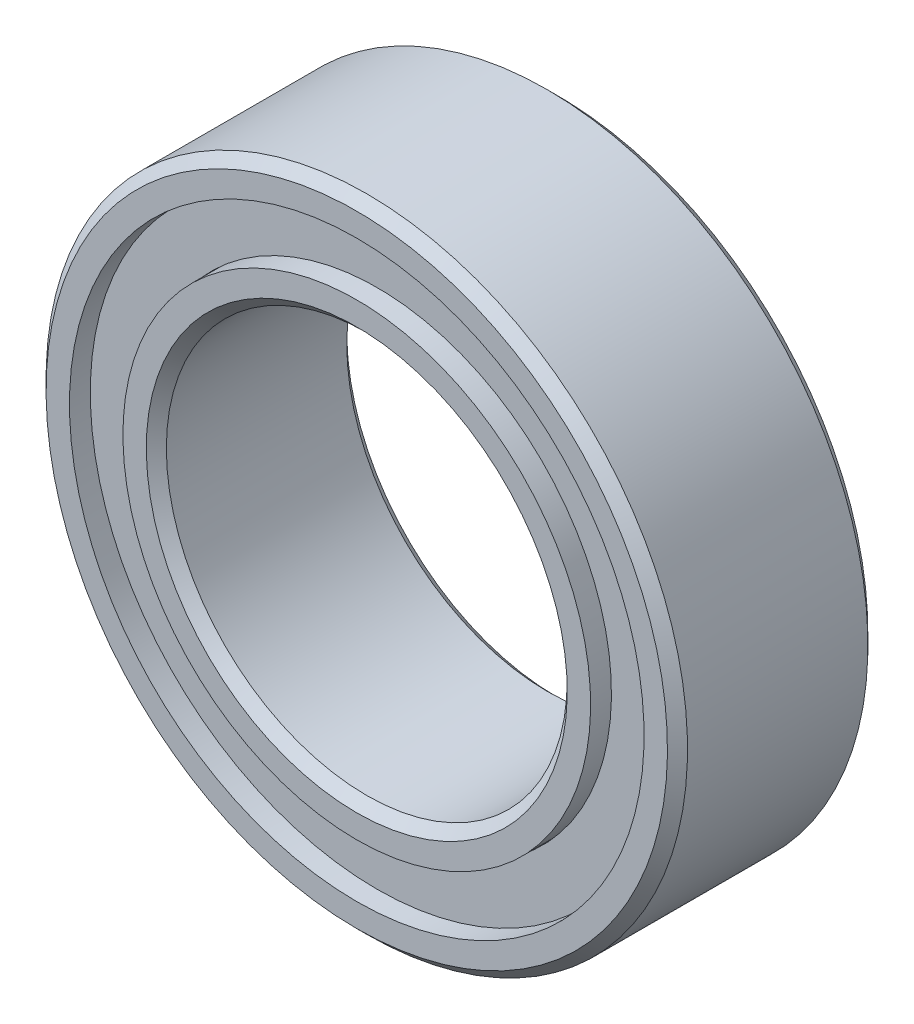
SolidWorks part; units mm, degrees
material "ASTM A36 Steel"
ref_plane "Front Plane" through (0, 0, 0) normal (0, 0, 1) x (1, 0, 0)
ref_plane "Top Plane" through (0, 0, 0) normal (0, 1, 0) x (1, 0, 0)
ref_plane "Right Plane" through (0, 0, 0) normal (1, 0, 0) x (0, 0, -1)
sketch "Sketch1" plane through (0, 0, 0) normal (0, 0, 1) x (1, 0, 0)
  circle A0 centre (0, 0) radius 16
  circle A1 centre (0, 0) radius 10
  dimension "OD" = 32
  dimension "ID" = 20
sketch "Sketch8" plane through (0, 0, 0) normal (1, 0, 0) x (0, 0, -1)
  line L1 (-5, 16) -> (5, 16)
  line L2 (-5, 16) -> (-5, -16)
  line L3 (-5, -16) -> (5, -16)
  line L4 (5, 16) -> (5, -16)
  line L5 (-5, 16) -> (5, -16) construction
  line L6 (-5, -16) -> (5, 16) construction
  point P0 (0, 0)
  point P6 (0, -16)
  dimension "Width" = 10
sketch "Sketch5" plane through (0, 0, 0) normal (1, 0, 0) x (0, 0, -1)
  line L0 (-5, 0) -> (5, 0) construction
  line L1 (0, 16) -> (0, -16) construction
  line L2 (4.5, 16) -> (-4.5, 16)
  line L3 (-4.5, 16) -> (-5, 15.5)
  line L4 (-5, 15.5) -> (-5, 14.3333)
  line L5 (-5, 14.3333) -> (-2.2222, 14.3333)
  line L6 (5, 14.3333) -> (2.2222, 14.3333)
  line L7 (5, 15.5) -> (5, 14.3333)
  line L8 (4.5, 16) -> (5, 15.5)
  line L9 (0, 16) -> (0, 13) construction
  line L10 (0, 13) -> (0, 10) construction
  line L11 (-2.5915, 13) -> (-5, 13) construction
  line L12 (3.6053, 11.6921) -> (3.9863, 11.6921)
  line L13 (-3.6053, 11.6921) -> (-3.9863, 11.6921)
  line L14 (-3.6053, 11.6921) -> (-3.6053, 14.3079)
  line L15 (-3.6053, 14.3079) -> (-3.9863, 14.3079)
  line L16 (-3.9863, 11.6921) -> (-3.9863, 14.3079)
  line L17 (-3.6053, 11.6921) -> (-3.9863, 14.3079) construction
  line L18 (-3.6053, 14.3079) -> (-3.9863, 11.6921) construction
  line L19 (3.9863, 11.6921) -> (3.9863, 14.3079)
  line L20 (3.6053, 14.3079) -> (3.9863, 14.3079)
  line L21 (3.6053, 11.6921) -> (3.6053, 14.3079)
  line L22 (0, 16) -> (0, -16) construction
  line L23 (5, 0) -> (5, 16) construction
  line L24 (5, 16) -> (4.5, 16) construction
  line L25 (-5, 0) -> (-5, 16) construction
  line L26 (-5, 16) -> (-4.5, 16) construction
  line L27 (5, 0) -> (5, -16) construction
  line L28 (-5, 0) -> (-5, -16) construction
  line L29 (-5, -16) -> (5, -16) construction
  arc A0 (-2.2222, 14.3333) -> (2.2222, 14.3333) centre (0, 13) cw
  circle A1 centre (0, 13) radius 2.5915 construction
  point P14 (0, 10)
  point P15 (-3.7958, 13)
  dimension "D1" = 45
  dimension "D2" = 0.5
  dimension "D3" = 4.4444
  dimension "D4" = 1.3333
  dimension "D5" = 0.381
  dimension "D6" = 0.0254
revolve "Revolve1" add sketch "Sketch5" angle 360 about L0
sketch "Sketch3" plane through (0, 0, 0) normal (1, 0, 0) x (0, 0, -1)
  line L0 (-5, 11.6667) -> (-2.2222, 11.6667)
  line L1 (0, 16) -> (0, -16) construction
  line L2 (-5, 15.5) -> (-5, 14.3333) construction
  line L3 (-5, 11.6667) -> (-5, 10.5)
  line L4 (-4.5, 16) -> (-5, 15.5) construction
  line L5 (-5, 10.5) -> (-4.5, 10)
  line L6 (-4.5, 10) -> (4.5, 10)
  line L7 (4.5, 16) -> (4.5, -16) construction
  line L8 (4.5, 10) -> (5, 10.5)
  line L9 (5, -15.5) -> (5, 15.5) construction
  line L10 (5, 10.5) -> (5, 11.6667)
  line L11 (5, 11.6667) -> (2.2222, 11.6667)
  line L13 (4.5, 16) -> (5, 15.5) construction
  arc A0 (2.2222, 14.3333) -> (-2.2222, 14.3333) centre (0, 13) ccw construction
  arc A1 (2.2222, 11.6667) -> (-2.2222, 11.6667) centre (0, 13) cw
revolve "Revolve3" add sketch "Sketch3" angle 360 about L0
sketch "Sketch4" plane through (0, 0, 0) normal (1, 0, 0) x (0, 0, -1)
  line L0 (-2.5915, 13) -> (2.5915, 13)
  arc A2 (-2.5915, 13) -> (2.5915, 13) centre (0, 13) cw
  arc A3 (2.2222, 14.3333) -> (-2.2222, 14.3333) centre (0, 13) ccw construction
revolve "Revolve4" add sketch "Sketch4" angle 360 about L0
pattern_circular "CirPattern1" count 13 every 27.692 about axis through (0, 0, 0) along (0, 0, 1) of bodies 104
equation "\"D2@Sketch5\" = \"Width@Sketch8\" * .05"
equation "\"D3@Sketch5\" = \"Width@Sketch8\" / 2.25"
equation "\"D4@Sketch5\"=((\"OD@Sketch1\"-\"ID@Sketch1\")/2)/4.5"
equation "\"D2@CirPattern1\" = 360/\"Balls@CirPattern1\""
